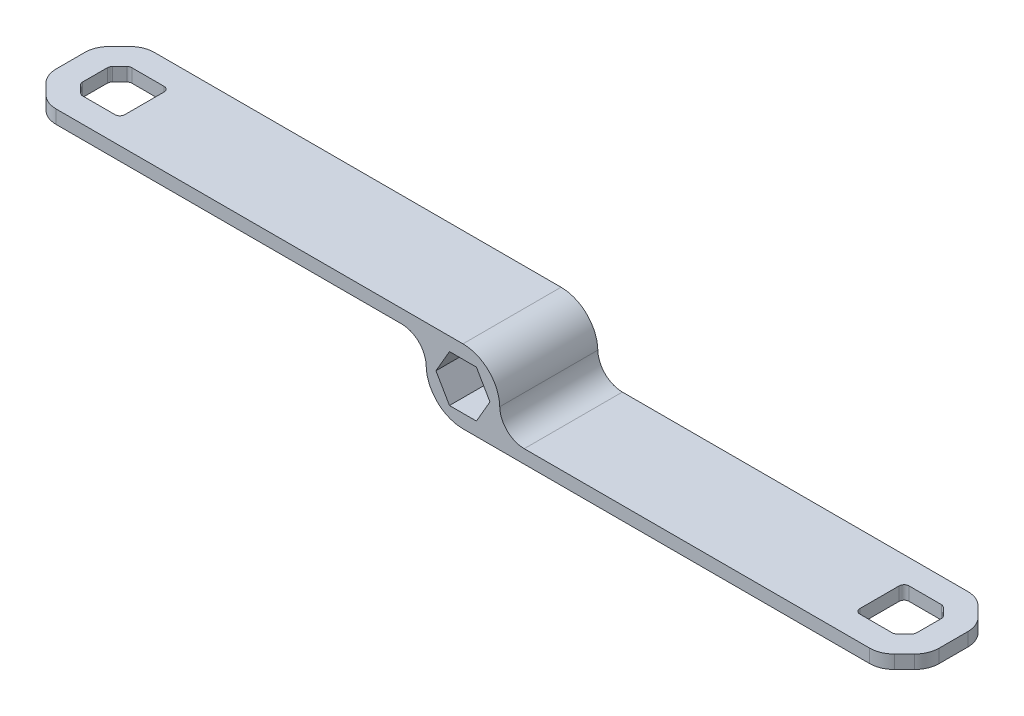
SolidWorks part; units mm, degrees
ref_plane "Front Plane" through (0, 0, 0) normal (0, 0, 1) x (1, 0, 0)
ref_plane "Top Plane" through (0, 0, 0) normal (0, 1, 0) x (1, 0, 0)
ref_plane "Right Plane" through (0, 0, 0) normal (1, 0, 0) x (0, 0, -1)
sketch "Sketch2" plane through (0, 0, 0) normal (0, 0, 1) x (1, 0, 0)
  line L1 (5.4993, 0) -> (2.7496, 4.7625)
  line L2 (2.7496, 4.7625) -> (-2.7496, 4.7625)
  line L3 (-2.7496, 4.7625) -> (-5.4993, 0)
  line L4 (-5.4993, 0) -> (-2.7496, -4.7625)
  line L5 (-2.7496, -4.7625) -> (2.7496, -4.7625)
  line L6 (2.7496, -4.7625) -> (5.4993, 0)
  circle A0 centre (0, 0) radius 4.7625 construction
  circle A1 centre (0, 0) radius 7.5
  dimension "D1" = 9.525
  dimension "D2" = 15
extrude "Boss-Extrude1" add sketch "Sketch2" along normal blind 20
ref_plane "Plane1" through (0, 0, 0) normal (-1, 0, 0) x (0, 0, 1)
sketch "Sketch3" plane through (0, 0, 0) normal (-1, 0, 0) x (0, 0, 1)
  line L0 (20, 4.7625) -> (0, 4.7625) construction
  line L1 (20, 4.7625) -> (0, 4.7625)
  line L2 (20, -7.5) -> (20, 7.5) construction
  line L3 (20, -7.5) -> (20, 7.5)
  line L4 (20, 7.5) -> (0, 7.5)
  line L5 (0, 7.5) -> (0, 4.7625)
extrude "Boss-Extrude2" add sketch "Sketch3" along normal blind 90 contours L4 L5 L1 L3
fillet "Fillet1" radius 5 1 edges at (-5.7938, 4.7625, 10)
chamfer "Chamfer1" distance 5 angle 45 2 edges at (-90, 6.1312, 0) (-90, 6.1312, 20)
fillet "Fillet2" radius 5 4 edges at (-85, 6.1312, 0) (-85, 6.1312, 20) (-90, 6.1312, 15) (-90, 6.1312, 5)
sketch "Sketch4" plane through (0, 7.5, 0) normal (0, 1, 0) x (1, 0, 0)
  line L6 (-74.9289, -15) -> (-74.9289, -5)
  line L12 (-5, -5) -> (-82.9289, -5)
  line L13 (-82.9289, -5) -> (-85, -7.0711)
  line L14 (-85, -7.0711) -> (-85, -12.9289)
  line L15 (-85, -12.9289) -> (-82.9289, -15)
  line L16 (-82.9289, -15) -> (-5, -15)
  line L17 (-5, -15) -> (-5, -5)
  line L18 (-74.9289, -5) -> (-82.9289, -5)
  line L19 (-82.9289, -5) -> (-85, -7.0711)
  line L20 (-85, -7.0711) -> (-85, -12.9289)
  line L21 (-85, -12.9289) -> (-82.9289, -15)
  line L22 (-82.9289, -15) -> (-74.9289, -15)
  dimension "D2" = 8
  dimension "D1" = 5
extrude "Cut-Extrude1" cut sketch "Sketch4" against normal blind 45
fillet "Fillet3" radius 1 6 edges at (-85, 6.1312, 7.0711) (-82.9289, 6.1312, 5) (-85, 6.1312, 12.9289) (-82.9289, 6.1312, 15) (-74.9289, 6.1312, 5) (-74.9289, 6.1312, 15)
ref_plane "Plane2" through (0, 0, 0) normal (0, 1, 0) x (1, 0, 0)
sketch "Sketch5" plane through (0, 0, 0) normal (-1, 0, 0) x (0, 0, 1)
  line L12 (0, 7.5) -> (0, -7.5) construction
  line L13 (0, 7.5) -> (0, -7.5)
  line L14 (0, -7.5) -> (20, -7.5)
  line L15 (20, -7.5) -> (20, -4.7625)
  line L16 (0, 0) -> (0, -4.7625)
  line L17 (20, 0) -> (0, 0)
  line L18 (20, -4.7625) -> (20, 0)
  line L19 (0, -4.7625) -> (20, -4.7625)
  line L20 (0, 0) -> (0, -4.7625)
  line L21 (20, 0) -> (0, 0)
  line L22 (20, -4.7625) -> (20, 0)
  line L23 (0, -4.7625) -> (20, -4.7625)
  dimension "D1" = 0
extrude "Boss-Extrude3" add sketch "Sketch5" against normal blind 90 contours L23 L13 L14 L15
chamfer "Chamfer2" distance 5 angle 45 2 edges at (90, -6.1312, 20) (90, -6.1312, 0)
fillet "Fillet4" radius 5 4 edges at (85, -6.1312, 20) (90, -6.1312, 15) (90, -6.1312, 5) (85, -6.1312, 0)
fillet "Fillet5" radius 5 1 edges at (5.7938, -4.7625, 10)
sketch "Sketch7" plane through (0, -7.5, 0) normal (0, -1, 0) x (1, 0, 0)
  line L6 (74.9289, 5) -> (74.9289, 15)
  line L12 (85, 12.9289) -> (82.9289, 15)
  line L13 (82.9289, 15) -> (5, 15)
  line L14 (5, 15) -> (5, 5)
  line L15 (5, 5) -> (82.9289, 5)
  line L16 (82.9289, 5) -> (85, 7.0711)
  line L17 (85, 7.0711) -> (85, 12.9289)
  line L18 (85, 12.9289) -> (82.9289, 15)
  line L19 (82.9289, 15) -> (74.9289, 15)
  line L21 (74.9289, 5) -> (82.9289, 5)
  line L22 (82.9289, 5) -> (85, 7.0711)
  line L23 (85, 7.0711) -> (85, 12.9289)
  dimension "D2" = 8
  dimension "D1" = 5
extrude "Cut-Extrude2" cut sketch "Sketch7" against normal blind 90
fillet "Fillet6" radius 1 6 edges at (74.9289, -6.1312, 15) (82.9289, -6.1312, 15) (85, -6.1312, 12.9289) (85, -6.1312, 7.0711) (82.9289, -6.1312, 5) (74.9289, -6.1312, 5)
